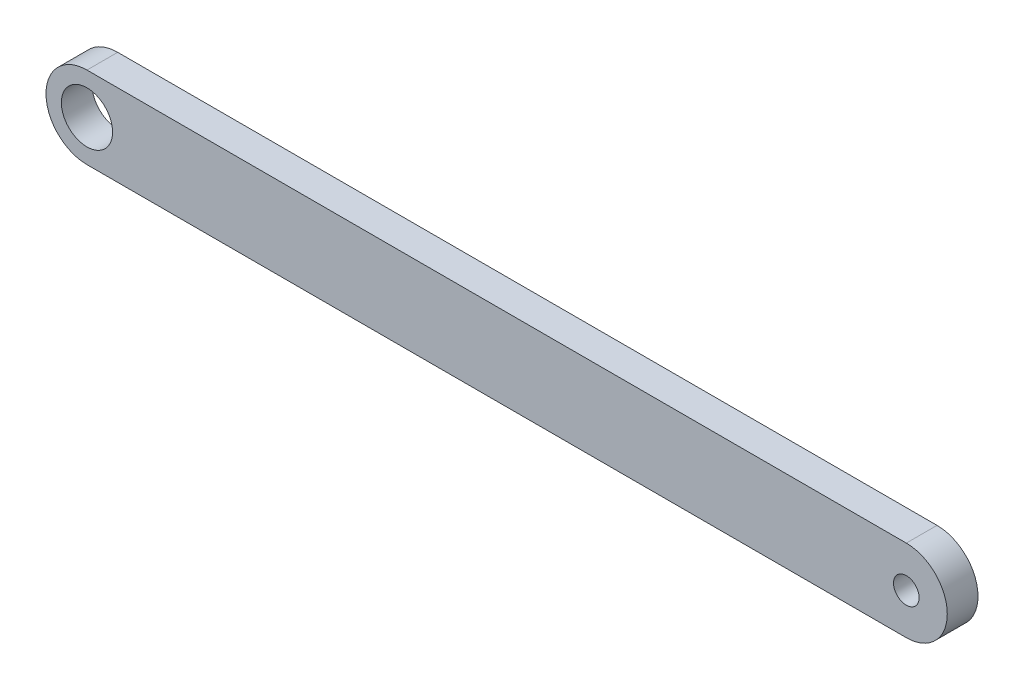
SolidWorks part; units mm, degrees
ref_plane "Alzado" through (0, 0, 0) normal (0, 0, 1) x (1, 0, 0)
ref_plane "Planta" through (0, 0, 0) normal (0, 1, 0) x (1, 0, 0)
ref_plane "Vista lateral" through (0, 0, 0) normal (1, 0, 0) x (0, 0, -1)
sketch "Croquis1" plane through (0, 0, 0) normal (0, 0, 1) x (1, 0, 0)
  line L0 (-54.371, 0) -> (105.629, 0) construction
  line L1 (-54.371, 8) -> (105.629, 8)
  line L2 (-54.371, -8) -> (105.629, -8)
  arc A0 (-54.371, 8) -> (-54.371, -8) centre (-54.371, 0) ccw
  arc A1 (105.629, -8) -> (105.629, 8) centre (105.629, 0) ccw
  circle A2 centre (-54.371, 0) radius 5
  circle A3 centre (105.629, 0) radius 2.5
  point P3 (25.629, 0)
  dimension "D2" = 8
  dimension "D3" = 10
  dimension "D4" = 5
  dimension "D1" = 160
extrude "Saliente-Extruir1" add sketch "Croquis1" along normal blind 6
